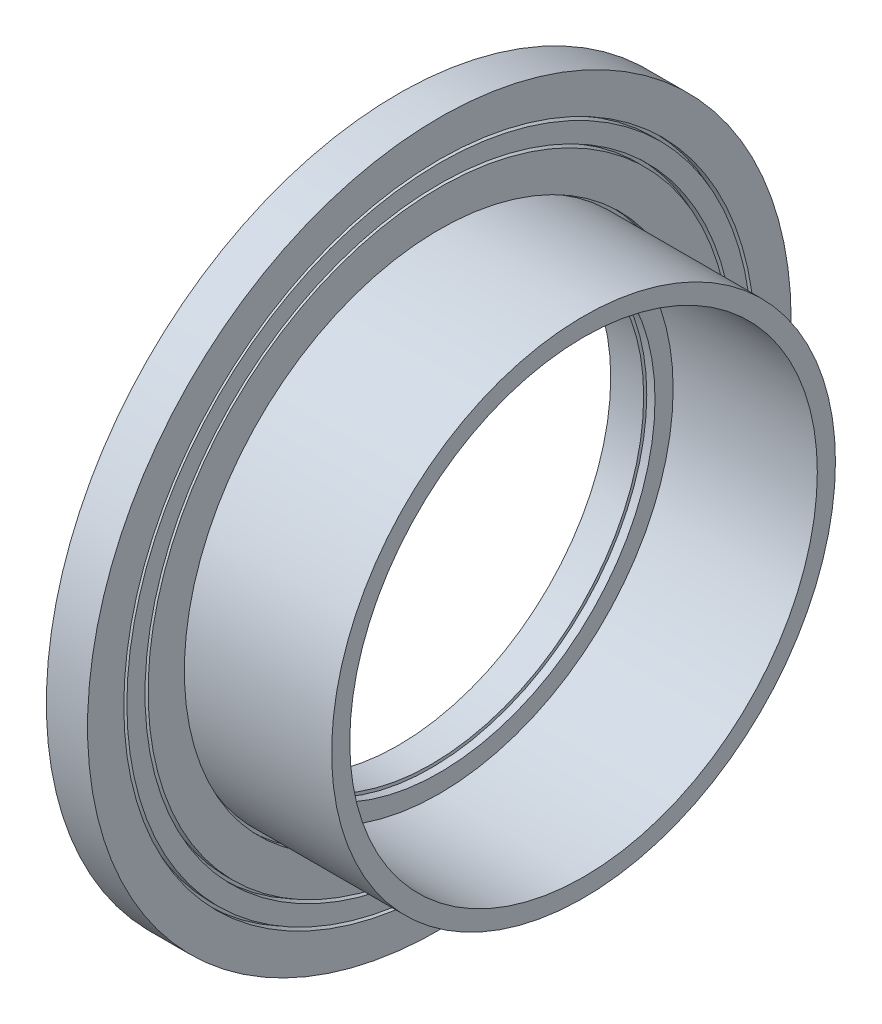
SolidWorks part; units mm, degrees
ref_plane "Front Plane" through (0, 0, 0) normal (0, 0, 1) x (1, 0, 0)
ref_plane "Top Plane" through (0, 0, 0) normal (0, 1, 0) x (1, 0, 0)
ref_plane "Right Plane" through (0, 0, 0) normal (1, 0, 0) x (0, 0, -1)
sketch "Sketch1" plane through (0, 0, 0) normal (1, 0, 0) x (0, 0, -1)
  circle A0 centre (0, 0) radius 17.08
  circle A1 centre (0, 0) radius 10.32
extrude "Boss-Extrude1" add sketch "Sketch1" along normal blind 2
sketch "Sketch2" plane through (2, 0, 0) normal (1, 0, 0) x (0, 0, -1)
  circle A1 centre (0, 0) radius 11.35
  circle A2 centre (0, 0) radius 12.23
  dimension "D1" = 0.88
extrude "Boss-Extrude2" add sketch "Sketch2" along normal blind 7
sketch "Sketch3" plane through (2, 0, 0) normal (1, 0, 0) x (0, 0, -1)
  circle A3 centre (0, 0) radius 10.32 construction
  circle A5 centre (0, 0) radius 10.47
  circle A6 centre (0, 0) radius 10.47
  circle A7 centre (0, 0) radius 10.32
  dimension "D1" = 1.76
extrude "Cut-Extrude1" cut sketch "Sketch3" against normal blind 0.4
sketch "Sketch12" plane through (2, 0, 0) normal (1, 0, 0) x (0, 0, -1)
  circle A1 centre (0, 0) radius 12.23 construction
  circle A2 centre (0, 0) radius 12.38
  circle A3 centre (0, 0) radius 12.38
  circle A4 centre (0, 0) radius 12.23
  dimension "D1" = 0.15
extrude "Cut-Extrude7" cut sketch "Sketch12" against normal blind 0.4
sketch "Sketch13" plane through (2, 0, 0) normal (1, 0, 0) x (0, 0, -1)
  circle A1 centre (0, 0) radius 14.29
  circle A2 centre (0, 0) radius 14.14
  circle A3 centre (0, 0) radius 14.14
  dimension "D1" = 1.76
  dimension "D2" = 0.15
extrude "Cut-Extrude8" cut sketch "Sketch13" against normal blind 0.4
sketch "Sketch14" plane through (2, 0, 0) normal (1, 0, 0) x (0, 0, -1)
  circle A1 centre (0, 0) radius 15.32
  circle A2 centre (0, 0) radius 15.17
  circle A3 centre (0, 0) radius 15.17
  dimension "D1" = 0.88
  dimension "D2" = 0.15
extrude "Cut-Extrude9" cut sketch "Sketch14" against normal blind 0.4
